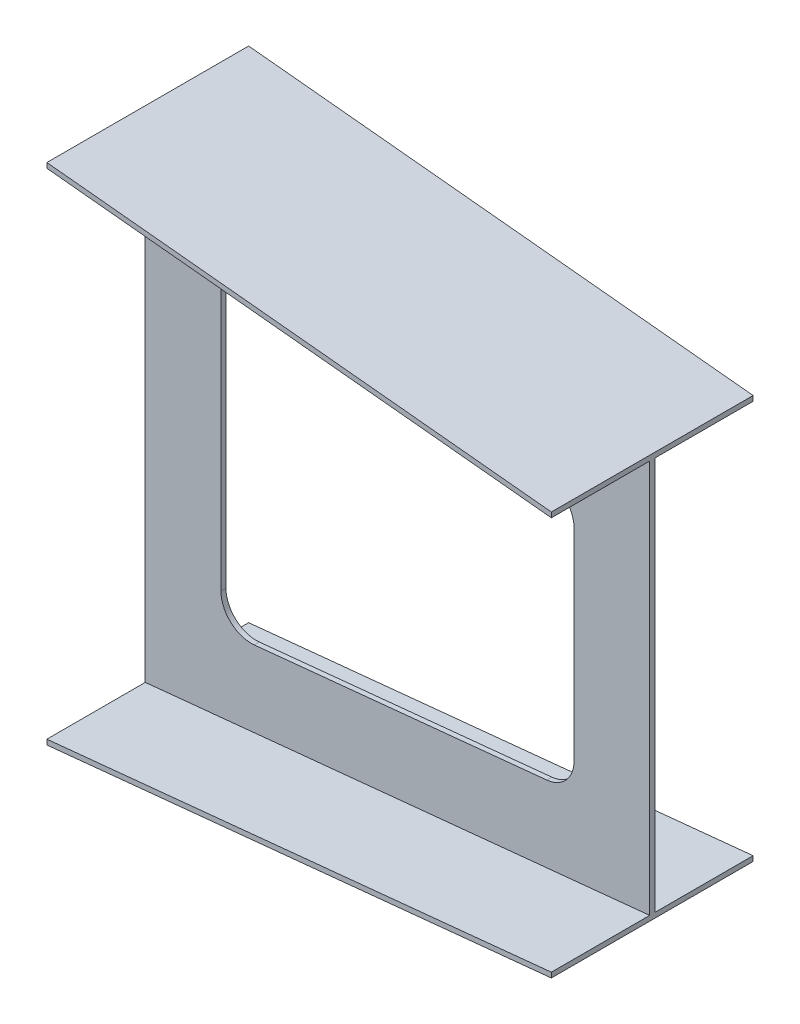
SolidWorks part; units mm, degrees
ref_plane "Front Plane" through (0, 0, 0) normal (0, 0, 1) x (1, 0, 0)
ref_plane "Top Plane" through (0, 0, 0) normal (0, 1, 0) x (1, 0, 0)
ref_plane "Right Plane" through (0, 0, 0) normal (1, 0, 0) x (0, 0, -1)
sketch "Sketch1" plane through (0, 0, 0) normal (1, 0, 0) x (0, 0, -1)
  line L1 (-205, 500) -> (195, 500)
  line L2 (-205, 500) -> (-205, 490)
  line L4 (195, 500) -> (195, 490)
  line L6 (-205, -490) -> (-205, -500)
  line L7 (-205, -500) -> (195, -500)
  line L8 (195, -490) -> (195, -500)
  line L15 (-205, -490) -> (-10, -490)
  line L16 (-5, 490) -> (-5, -490) construction
  line L18 (-205, 490) -> (-10, 490)
  line L19 (0, 0) -> (192.2403, 0) construction
  line L21 (-10, 490) -> (-10, -490)
  line L23 (0, 490) -> (0, -490)
  line L27 (0, 490) -> (195, 490)
  line L28 (0, -490) -> (195, -490)
  dimension "D1" = 400
  dimension "D2" = 10
  dimension "D3" = 1000
  dimension "D4" = 10
ref_plane "Plane2" through (1000, 0, 0) normal (1, 0, 0) x (0, 0, -1)
sketch "Sketch4" plane through (1000, 0, -1000) normal (-1, 0, 0) x (0, 0, 1)
  line L1 (805, 400) -> (1205, 400)
  line L2 (805, 400) -> (805, 390)
  line L4 (1205, 400) -> (1205, 390)
  line L6 (805, -390) -> (805, -400)
  line L7 (805, -400) -> (1205, -400)
  line L8 (1205, -390) -> (1205, -400)
  line L15 (805, -390) -> (1000, -390)
  line L16 (1005, 390) -> (1005, -390) construction
  line L18 (805, 390) -> (1000, 390)
  line L19 (1010, -390) -> (1205, -390)
  line L21 (1000, 390) -> (1000, -390)
  line L23 (1010, 390) -> (1010, -390)
  line L24 (1010, 390) -> (1205, 390)
  line L26 (1010, 490) -> (1010, -490) construction
  line L27 (1000, 0) -> (820.2065, 0) construction
  dimension "D1" = 400
  dimension "D2" = 10
  dimension "D3" = 800
  dimension "D4" = 10
loft "Loft4" add profiles "Sketch1", "Sketch4"
sketch "Sketch6" plane through (0, 0, 10) normal (0, 0, 1) x (1, 0, 0)
  line L8 (150, -324.2519) -> (850, -254.2519)
  line L9 (850, -254.2519) -> (850, 254.2519)
  line L10 (850, 254.2519) -> (150, 324.2519)
  line L11 (150, 324.2519) -> (150, -324.2519)
  line L12 (215.9702, -317.6548) -> (795.9702, -259.6548)
  line L13 (850, -199.9526) -> (850, 199.9526)
  line L14 (795.9702, 259.6548) -> (215.9702, 317.6548)
  line L15 (150, 257.9526) -> (150, -257.9526)
  arc A0 (150, -257.9526) -> (215.9702, -317.6548) centre (210, -257.9526) ccw
  arc A1 (850, 199.9526) -> (795.9702, 259.6548) centre (790, 199.9526) ccw
  arc A2 (850, -199.9526) -> (795.9702, -259.6548) centre (790, -199.9526) cw
  arc A3 (150, 257.9526) -> (215.9702, 317.6548) centre (210, 257.9526) cw
  dimension "D2" = 60
  dimension "D1" = 150
extrude "Cut-Extrude1" cut sketch "Sketch6" against normal blind 10
